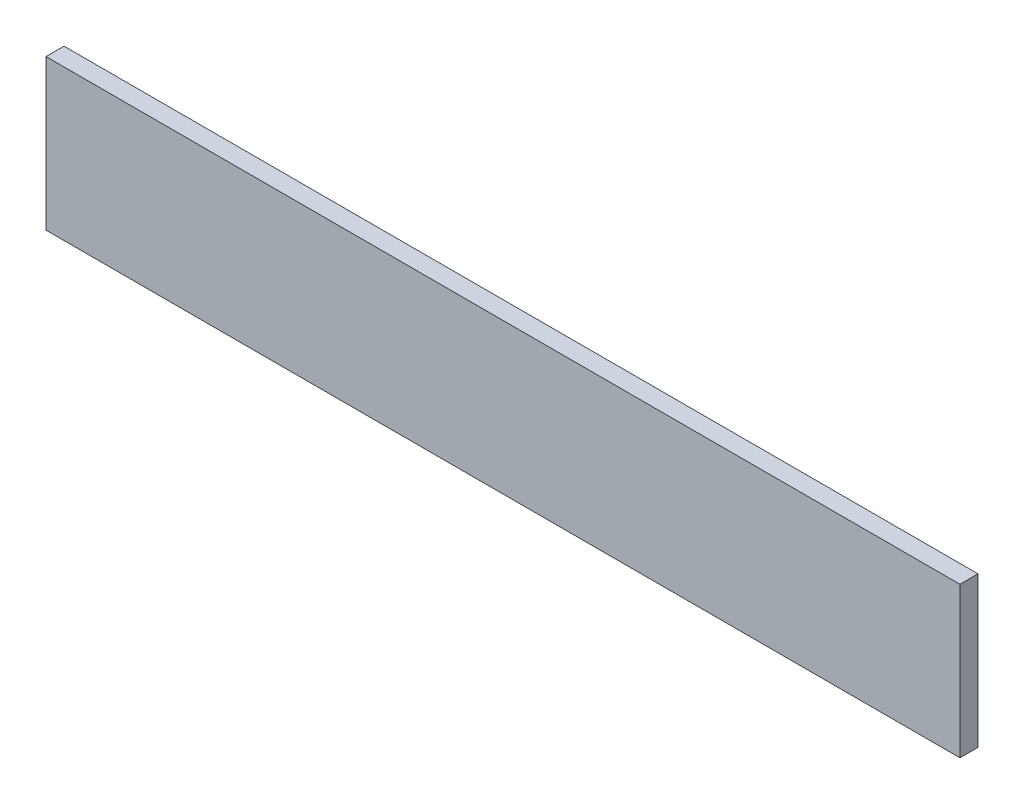
SolidWorks part; units mm, degrees
material "Balsa"
ref_plane "Front Plane" through (0, 0, 0) normal (0, 0, 1) x (1, 0, 0)
ref_plane "Top Plane" through (0, 0, 0) normal (0, 1, 0) x (1, 0, 0)
ref_plane "Right Plane" through (0, 0, 0) normal (1, 0, 0) x (0, 0, -1)
sketch "Sketch1" plane through (0, 0, 0) normal (0, 0, 1) x (1, 0, 0)
  line L1 (-380, -62.5) -> (380, -62.5)
  line L2 (-380, -62.5) -> (-380, 62.5)
  line L3 (-380, 62.5) -> (380, 62.5)
  line L4 (380, -62.5) -> (380, 62.5)
  line L5 (-380, -62.5) -> (380, 62.5) construction
  line L6 (-380, 62.5) -> (380, -62.5) construction
  point P0 (0, 0)
  dimension "D1" = 760
  dimension "D2" = 125
extrude "Boss-Extrude1" add sketch "Sketch1" along normal blind 15
